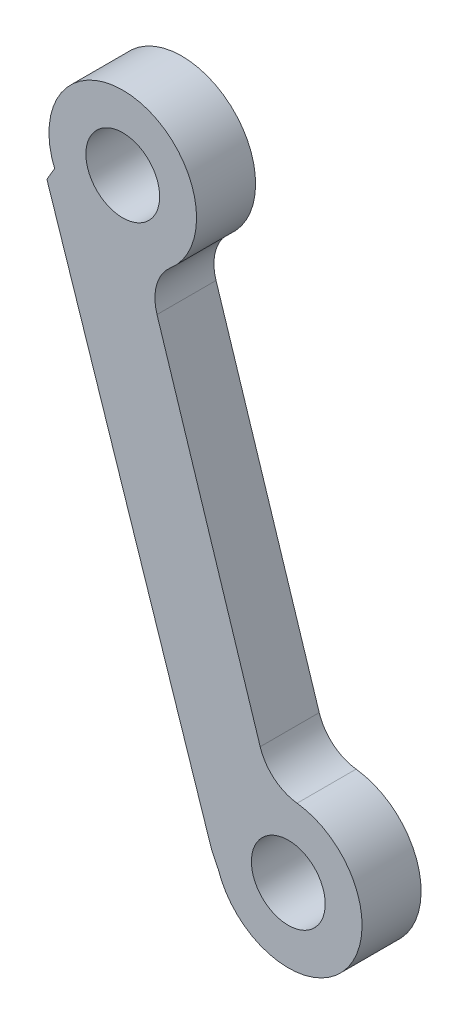
SolidWorks part; units mm, degrees
material "PLA"
ref_plane "Front Plane" through (0, 0, 0) normal (0, 0, 1) x (1, 0, 0)
ref_plane "Top Plane" through (0, 0, 0) normal (0, 1, 0) x (1, 0, 0)
ref_plane "Right Plane" through (0, 0, 0) normal (1, 0, 0) x (0, 0, -1)
sketch "Sketch1" plane through (0, 0, 0) normal (0, 0, 1) x (1, 0, 0)
  line L0 (124.38, 516.941) -> (697.7134, 516.941) construction
  line L7 (15.0111, 49.8307) -> (3.8387, 83.6229)
  line L10 (10.5731, 81.687) -> (18.8981, 55.6504)
  line L13 (3.8387, 83.6229) -> (4.3612, 84.5098)
  line L16 (18.8981, 55.6504) -> (18.9693, 55.369)
  line L17 (15.0111, 49.8307) -> (15.4551, 48.9286)
  circle A7 centre (8.9794, 86.4262) radius 2.5
  circle A8 centre (20.1946, 50.5214) radius 2.5
  arc A9 (10.5731, 81.687) -> (4.3612, 84.5098) centre (8.9794, 86.4262) ccw
  arc A11 (15.4551, 48.9286) -> (18.9693, 55.369) centre (20.1946, 50.5214) ccw
extrude "Boss-Extrude1" add sketch "Sketch1" along normal blind 4
fillet "Fillet2" radius 3 2 edges at (18.9693, 55.369, 2) (10.5731, 81.687, 2)
